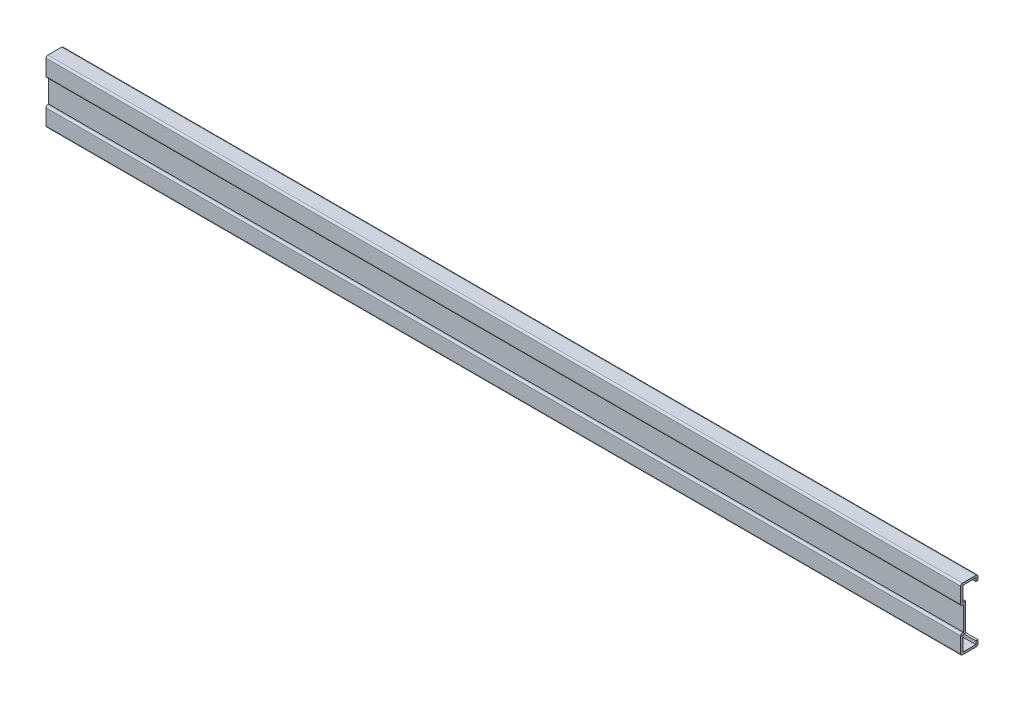
SolidWorks part; units mm, degrees
ref_plane "Спереди" through (0, 0, 0) normal (0, 0, 1) x (1, 0, 0)
ref_plane "Сверху" through (0, 0, 0) normal (0, 1, 0) x (1, 0, 0)
ref_plane "Справа" through (0, 0, 0) normal (1, 0, 0) x (0, 0, -1)
sketch "Эскиз1" plane through (0, 0, 0) normal (1, 0, 0) x (0, 0, -1)
  line L0 (0, 6.5) -> (0, -6.5)
  line L1 (-12.4481, 0) -> (26.4522, 0) construction
  line L2 (0, -6.5) -> (-0.5, -6.5)
  line L3 (-1.5, -7.5) -> (-1.5, -16)
  line L4 (-0.5, -17) -> (7, -17)
  line L5 (8, -16) -> (8, -14)
  line L6 (8, 16) -> (8, 14)
  line L7 (-0.5, 17) -> (7, 17)
  line L8 (-1.5, 7.5) -> (-1.5, 16)
  line L9 (0, 6.5) -> (-0.5, 6.5)
  arc A0 (7, -17) -> (8, -16) centre (7, -16) ccw
  arc A1 (-1.5, -7.5) -> (-0.5, -6.5) centre (-0.5, -7.5) cw
  arc A2 (-1.5, 16) -> (-0.5, 17) centre (-0.5, 16) cw
  arc A3 (-1.5, -16) -> (-0.5, -17) centre (-0.5, -16) ccw
  arc A4 (-1.5, 7.5) -> (-0.5, 6.5) centre (-0.5, 7.5) ccw
  arc A5 (7, 17) -> (8, 16) centre (7, 16) cw
  point P14 (0, 0)
  point P16 (8, -17)
  point P20 (0, 0)
  point P26 (-1.5, -17)
  point P30 (0, 0)
  dimension "D1" = 1
  dimension "D2" = 1
extrude "Вытянуть-Тонкостенный3" add sketch "Эскиз1" along normal blind 500 thin
